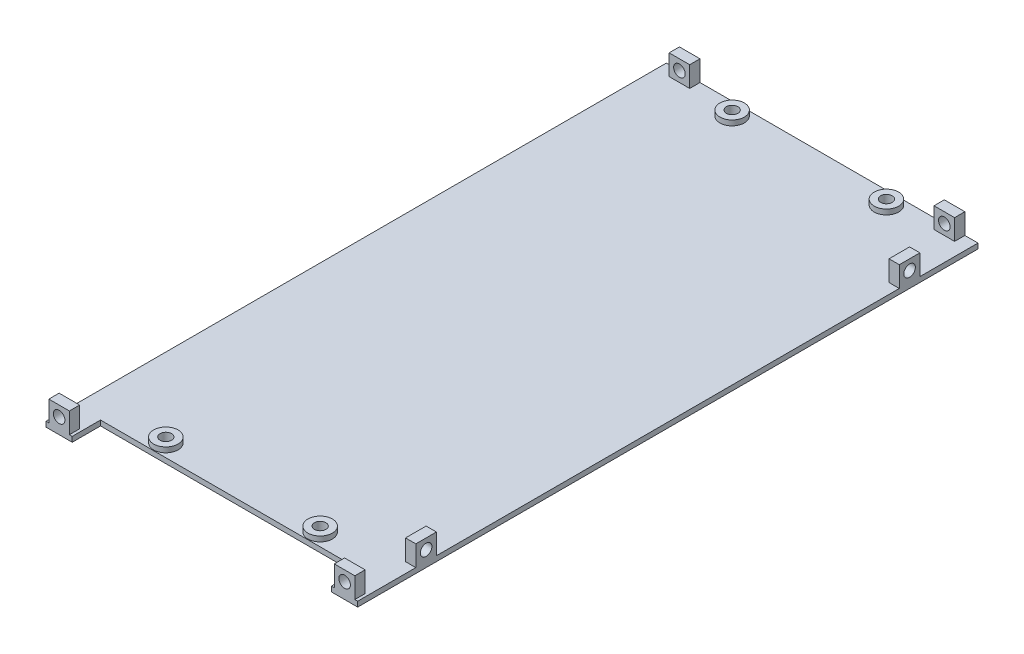
SolidWorks part; units mm, degrees
ref_plane "Front Plane" through (0, 0, 0) normal (0, 0, 1) x (1, 0, 0)
ref_plane "Top Plane" through (0, 0, 0) normal (0, 1, 0) x (1, 0, 0)
ref_plane "Right Plane" through (0, 0, 0) normal (1, 0, 0) x (0, 0, -1)
sketch "Sketch1" plane through (0, 0, 0) normal (0, 1, 0) x (1, 0, 0)
  line L0 (0, 0) -> (11, 0) construction
  line L2 (0, 0) -> (0, 242) construction
  line L3 (0, 242) -> (122, 242) construction
  line L4 (122, 0) -> (122, 242) construction
  line L5 (0.4, 241.6) -> (121.6, 241.6)
  line L6 (0.4, 241.6) -> (0.4, 0.4)
  line L8 (121.6, 241.6) -> (121.6, 0.4)
  line L9 (11, 0) -> (11, 11) construction
  line L10 (11, 11) -> (111, 11) construction
  line L11 (111, 11) -> (111, 0) construction
  line L12 (111, 0) -> (122, 0) construction
  line L13 (0.4, 0.4) -> (10.6, 0.4)
  line L14 (10.6, 0.4) -> (10.6, 11.4)
  line L15 (10.6, 11.4) -> (111.4, 11.4)
  line L16 (111.4, 11.4) -> (111.4, 0.4)
  line L17 (111.4, 0.4) -> (121.6, 0.4)
  dimension "D1" = 242
  dimension "D3" = 0.4
  dimension "D4" = 0.4
  dimension "D5" = 0.4
  dimension "D6" = 122
  dimension "D7" = 100
  dimension "D8" = 11
  dimension "D9" = 0.4
  dimension "D10" = 0.4
  dimension "D11" = 0.4
  dimension "D12" = 0.4
  dimension "D13" = 0.4
extrude "Boss-Extrude1" add sketch "Sketch1" along normal blind 2
sketch "Sketch2" plane through (0, 2, 0) normal (0, 1, 0) x (1, 0, 0)
  line L5 (121.6, 241.6) -> (0.4, 241.6) construction
  line L6 (5.5, 241.6) -> (13.5, 241.6)
  line L7 (5.5, 241.6) -> (5.5, 237.6)
  line L8 (5.5, 237.6) -> (13.5, 237.6)
  line L9 (13.5, 241.6) -> (13.5, 237.6)
  line L10 (0.4, 121) -> (121.6, 121) construction
  line L19 (0.4, 241.6) -> (0.4, 0.4) construction
  line L20 (121.6, 0.4) -> (121.6, 241.6) construction
  line L21 (61, 241.6) -> (61, 11.4) construction
  line L22 (10.6, 11.4) -> (111.4, 11.4) construction
  line L23 (116.5, 237.6) -> (108.5, 237.6)
  line L24 (108.5, 241.6) -> (108.5, 237.6)
  line L25 (116.5, 241.6) -> (108.5, 241.6)
  line L26 (116.5, 241.6) -> (116.5, 237.6)
  line L31 (0.4, 0.4) -> (10.6, 0.4) construction
  line L32 (1.5, 0.4) -> (9.5, 0.4)
  line L33 (1.5, 0.4) -> (1.5, 4.4)
  line L34 (1.5, 4.4) -> (9.5, 4.4)
  line L35 (9.5, 0.4) -> (9.5, 4.4)
  line L36 (120.5, 4.4) -> (112.5, 4.4)
  line L37 (112.5, 0.4) -> (112.5, 4.4)
  line L38 (120.5, 0.4) -> (112.5, 0.4)
  line L39 (120.5, 0.4) -> (120.5, 4.4)
  line L40 (121.6, 31) -> (117.6, 31)
  line L41 (121.6, 219) -> (117.6, 219)
  line L42 (121.6, 219) -> (121.6, 211)
  line L43 (121.6, 211) -> (117.6, 211)
  line L44 (117.6, 219) -> (117.6, 211)
  line L45 (117.6, 23) -> (117.6, 31)
  line L46 (121.6, 23) -> (117.6, 23)
  line L47 (121.6, 23) -> (121.6, 31)
  point P18 (9.5, 241.6)
  point P19 (112.5, 241.6)
  point P36 (5.5, 0.4)
  point P37 (5.5, 0.4)
  point P42 (121.6, 215)
  point P43 (121.6, 27)
  dimension "D1" = 4
  dimension "D2" = 8
  dimension "D3" = 188
  dimension "D4" = 103
extrude "Boss-Extrude2" add sketch "Sketch2" along normal blind 8
sketch "Sketch3" plane through (0, 0, -0.4) normal (0, 0, 1) x (1, 0, 0)
  line L0 (112.5, 10) -> (120.5, 10) construction
  line L1 (112.5, 10) -> (112.5, 2) construction
  line L2 (1.5, 10) -> (9.5, 10) construction
  line L3 (9.5, 10) -> (9.5, 2) construction
  circle A0 centre (5.5, 6) radius 2.25
  circle A1 centre (116.5, 6) radius 2.25
  point P7 (116.5, 10)
  point P11 (112.5, 6)
  point P14 (5.5, 10)
  point P17 (9.5, 6)
  dimension "D1" = 4.5
extrude "Cut-Extrude1" cut sketch "Sketch3" against normal up to next
sketch "Sketch5" plane through (0, 0, -241.6) normal (0, 0, -1) x (-1, 0, 0)
  line L0 (-116.5, 10) -> (-108.5, 10) construction
  line L1 (-108.5, 10) -> (-108.5, 2) construction
  line L2 (-13.5, 10) -> (-5.5, 10) construction
  line L3 (-13.5, 10) -> (-13.5, 2) construction
  circle A0 centre (-112.5, 6) radius 2.25
  circle A1 centre (-9.5, 6) radius 2.25
  point P6 (-112.5, 10)
  point P9 (-108.5, 6)
  point P12 (-9.5, 10)
  point P15 (-13.5, 6)
  dimension "D1" = 4.5
extrude "Cut-Extrude3" cut sketch "Sketch5" against normal up to next
sketch "Sketch6" plane through (121.6, 0, 0) normal (1, 0, 0) x (0, 0, -1)
  line L0 (23, 10) -> (31, 10) construction
  line L1 (31, 10) -> (31, 2) construction
  line L2 (211, 10) -> (219, 10) construction
  line L3 (211, 10) -> (211, 2) construction
  circle A0 centre (27, 6) radius 2.25
  circle A1 centre (215, 6) radius 2.25
  point P6 (27, 10)
  point P9 (31, 6)
  point P12 (215, 10)
  point P15 (211, 6)
  dimension "D1" = 4.5
extrude "Cut-Extrude4" cut sketch "Sketch6" against normal up to next
sketch "Sketch7" plane through (0, 0, 0) normal (0, -1, 0) x (1, 0, 0)
  line L0 (61, -11.4) -> (61, -241.6) construction
  line L1 (10.6, -11.4) -> (111.4, -11.4) construction
  line L2 (121.6, -241.6) -> (0.4, -241.6) construction
  circle A0 centre (31, -236.6) radius 2.25
  circle A1 centre (31, -16.4) radius 2.25
  circle A2 centre (91, -236.6) radius 2.25
  circle A3 centre (91, -16.4) radius 2.25
  circle A4 centre (31, -236.6) radius 4.75
  circle A5 centre (31, -16.4) radius 4.75
  circle A6 centre (91, -236.6) radius 4.75
  circle A7 centre (91, -16.4) radius 4.75
  dimension "D1" = 4.5
  dimension "D6" = 2.5
  dimension "D2" = 60
  dimension "D3" = 5
  dimension "D4" = 5
extrude "Boss-Extrude3" add sketch "Sketch7" against normal blind 4
sketch "Sketch8" plane through (0, 4, 0) normal (0, 1, 0) x (1, 0, 0)
  circle A2 centre (31, 16.4) radius 2.25
  circle A3 centre (31, 16.4) radius 2.25
  circle A5 centre (91, 16.4) radius 2.25
  circle A6 centre (91, 16.4) radius 2.25
  circle A8 centre (31, 236.6) radius 2.25
  circle A9 centre (31, 236.6) radius 2.25
  circle A11 centre (91, 236.6) radius 2.25
  circle A12 centre (91, 236.6) radius 2.25
  dimension "D1" = 0
  dimension "D2" = 0
  dimension "D3" = 0
  dimension "D4" = 0
extrude "Cut-Extrude5" cut sketch "Sketch8" against normal up to next
